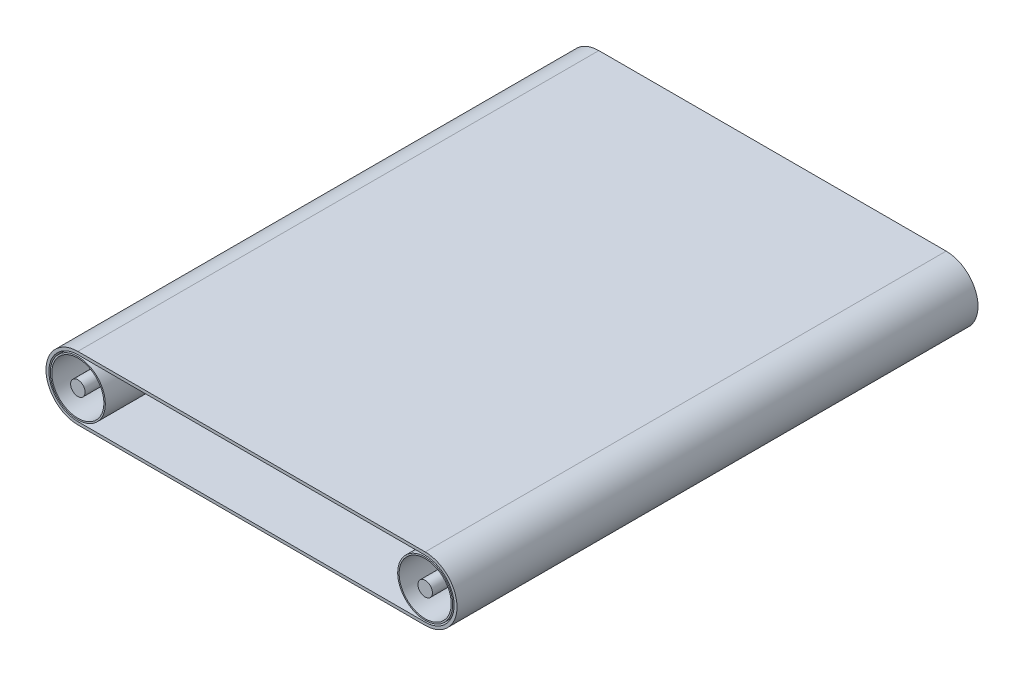
SolidWorks part; units mm, degrees
ref_plane "Plan de face" through (0, 0, 0) normal (0, 0, 1) x (1, 0, 0)
ref_plane "Plan de dessus" through (0, 0, 0) normal (0, 1, 0) x (1, 0, 0)
ref_plane "Plan de droite" through (0, 0, 0) normal (1, 0, 0) x (0, 0, -1)
sketch "Esquisse1" plane through (0, 0, 0) normal (0, 0, 1) x (1, 0, 0)
  line L0 (0, 0) -> (120, 0)
  line L1 (120, 20) -> (0, 20)
  line L2 (0, 21) -> (120, 21)
  line L3 (120, -1) -> (0, -1)
  arc A0 (120, 0) -> (120, 20) centre (120, 10) ccw
  arc A1 (0, 20) -> (0, 0) centre (0, 10) ccw
  arc A2 (120, 21) -> (120, -1) centre (120, 10) cw
  arc A3 (0, -1) -> (0, 21) centre (0, 10) cw
  dimension "D1" = 10
  dimension "D2" = 120
  dimension "D3" = 1
  dimension "D5" = 120
  dimension "D4" = 1
extrude "Boss.-Extru.1" add sketch "Esquisse1" along normal blind 180
sketch "Esquisse2" plane through (0, 0, 180) normal (0, 0, 1) x (1, 0, 0)
  line L0 (60, 48.8331) -> (60, -29.1694) construction
  circle A0 centre (0, 10) radius 2.5
  circle A1 centre (120, 10) radius 2.5
  dimension "D1" = 5
  dimension "D2" = 60
extrude "Boss.-Extru.2" add sketch "Esquisse2" against normal blind 180 separate body
sketch "Esquisse3" plane through (0, 0, 180) normal (0, 0, 1) x (1, 0, 0)
  line L0 (60, 44.3818) -> (60, -18.2819) construction
  circle A0 centre (0, 10) radius 9.5
  circle A1 centre (0, 10) radius 9
  circle A2 centre (120, 10) radius 9
  circle A3 centre (120, 10) radius 9.5
  dimension "D1" = 19
  dimension "D2" = 18
  dimension "D3" = 60
extrude "Boss.-Extru.3" add sketch "Esquisse3" against normal blind 180 separate body
